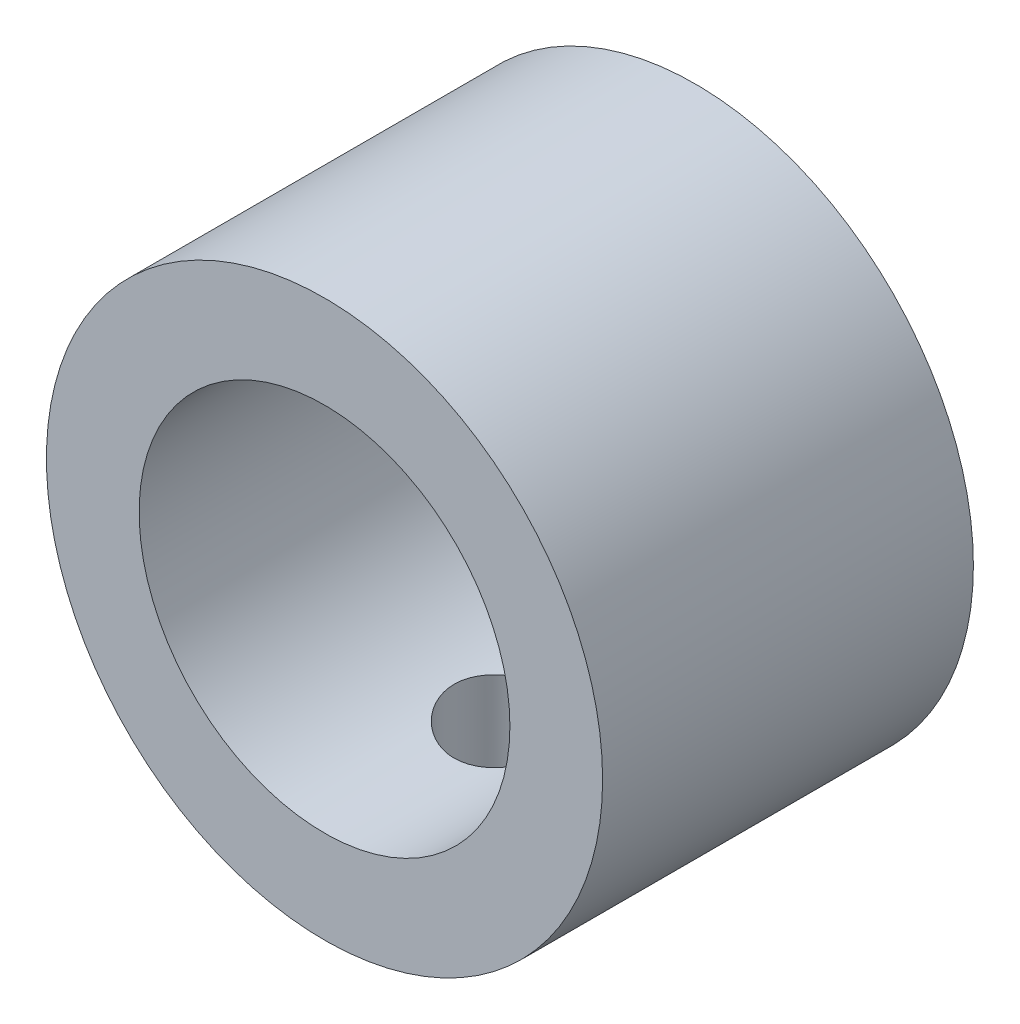
SolidWorks part; units mm, degrees
ref_plane "Front Plane" through (0, 0, 0) normal (0, 0, 1) x (1, 0, 0)
ref_plane "Top Plane" through (0, 0, 0) normal (0, 1, 0) x (1, 0, 0)
ref_plane "Right Plane" through (0, 0, 0) normal (1, 0, 0) x (0, 0, -1)
sketch "Sketch1" plane through (0, 0, 0) normal (0, 0, 1) x (1, 0, 0)
  circle A0 centre (0, 0) radius 7.5
  circle A1 centre (0, 0) radius 5
  dimension "D1" = 15
  dimension "D2" = 10
extrude "Boss-Extrude1" add sketch "Sketch1" along normal mid plane 10
sketch "Sketch2" plane through (0, 0, 0) normal (0, 1, 0) x (1, 0, 0)
  circle A0 centre (0, 0) radius 1.5
  dimension "D1" = 3
extrude "Cut-Extrude1" cut sketch "Sketch2" against normal up to surface (7.5 mm away)
